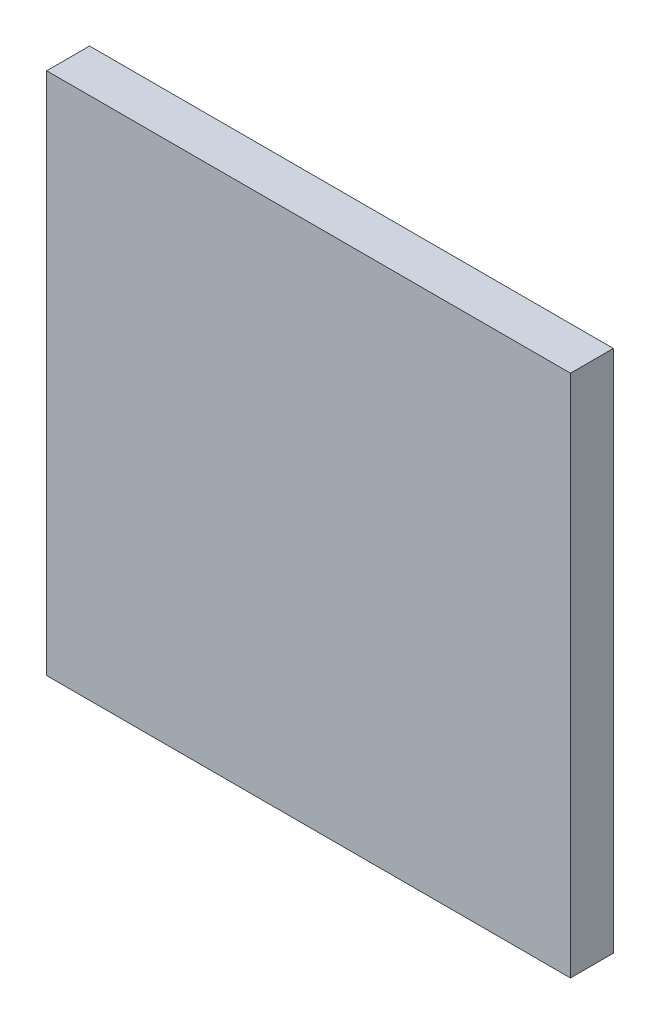
SolidWorks part; units mm, degrees
ref_plane "Front Plane" through (0, 0, 0) normal (0, 0, 1) x (1, 0, 0)
ref_plane "Top Plane" through (0, 0, 0) normal (0, 1, 0) x (1, 0, 0)
ref_plane "Right Plane" through (0, 0, 0) normal (1, 0, 0) x (0, 0, -1)
sketch "Sketch1" plane through (0, 0, 0) normal (0, 0, 1) x (1, 0, 0)
  line L1 (-28.1, -28.1) -> (28.1, -28.1)
  line L2 (-28.1, -28.1) -> (-28.1, 28.1)
  line L3 (-28.1, 28.1) -> (28.1, 28.1)
  line L4 (28.1, -28.1) -> (28.1, 28.1)
  line L5 (-28.1, -28.1) -> (28.1, 28.1) construction
  line L6 (-28.1, 28.1) -> (28.1, -28.1) construction
  point P0 (0, 0)
  dimension "D1" = 56.2
  dimension "D2" = 56.2
extrude "Boss-Extrude1" add sketch "Sketch1" along normal blind 4.6
equation "\"mat\"=\"mat@levv1.assembly\""
equation "\"D1@Sketch1\"=80-3*\"mat\"-10"
equation "\"D2@Sketch1\" = \"D1@Sketch1\""
equation "\"D1@Boss-Extrude1\"=\"mat\""
